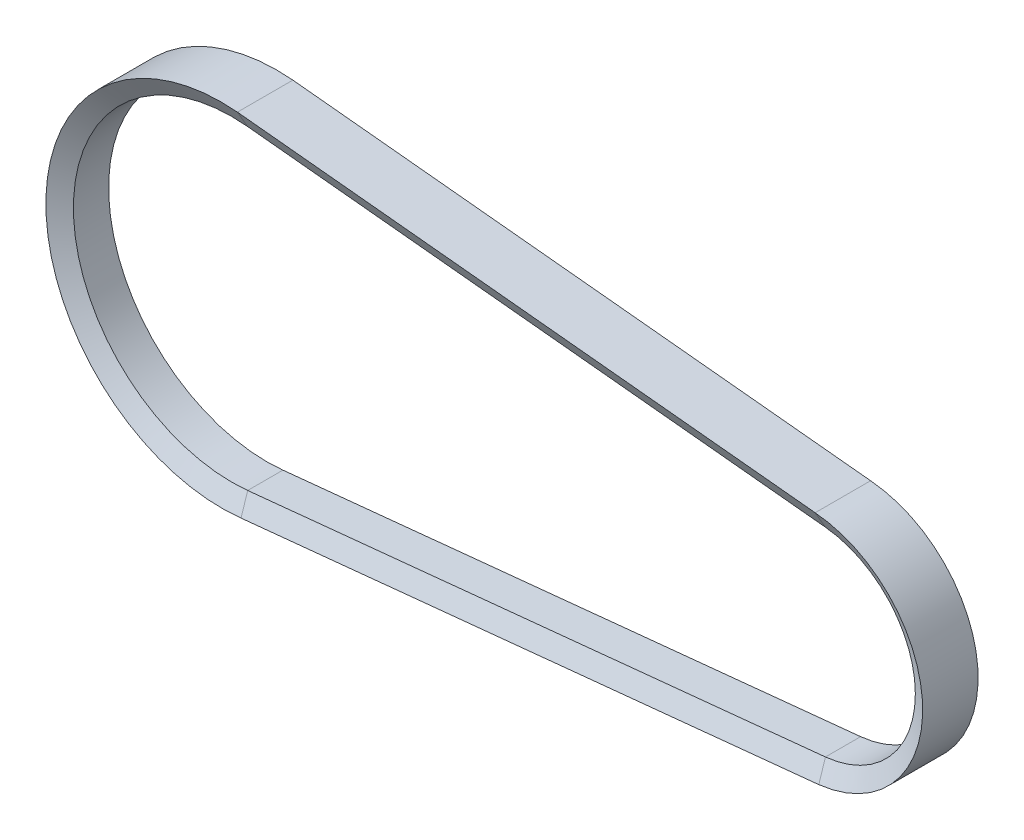
SolidWorks part; units mm, degrees
ref_plane "Front Plane" through (0, 0, 0) normal (0, 0, 1) x (1, 0, 0)
ref_plane "Top Plane" through (0, 0, 0) normal (0, 1, 0) x (1, 0, 0)
ref_plane "Right Plane" through (0, 0, 0) normal (1, 0, 0) x (0, 0, -1)
sketch "Sketch2" plane through (0, 0, 0) normal (0, 0, 1) x (1, 0, 0)
  line L0 (0, 0) -> (1, 0) construction
  line L1 (0, 0) -> (0, 1) construction
  line L2 (5.4, 53.7293) -> (203.4, 33.8296)
  line L3 (203.4, -33.8296) -> (5.4, -53.7293)
  arc A0 (5.4, -53.7293) -> (5.4, 53.7293) centre (0, 0) cw
  arc A1 (203.4, 33.8296) -> (203.4, -33.8296) centre (200, 0) cw
ref_plane "Plane1" through (5.4, 0, 0) normal (1, 0, 0) x (0, 0, -1)
sketch "Sketch3" plane through (5.4, 0, 0) normal (1, 0, 0) x (0, 0, -1)
  line L0 (-5.5794, 54) -> (6.4906, 54)
  line L1 (-5.5794, 54) -> (-9.0435, 60)
  line L2 (-9.0435, 60) -> (9.9547, 60)
  line L3 (9.9547, 60) -> (6.4906, 54)
  point P3 (0.4556, 54)
  dimension "D1" = 6.035
  dimension "D2" = 54
  dimension "D3" = 6
  dimension "D4" = 60
  dimension "D5" = 60
sweep "Sweep1" add profiles "Sketch3" path "Sketch2"
